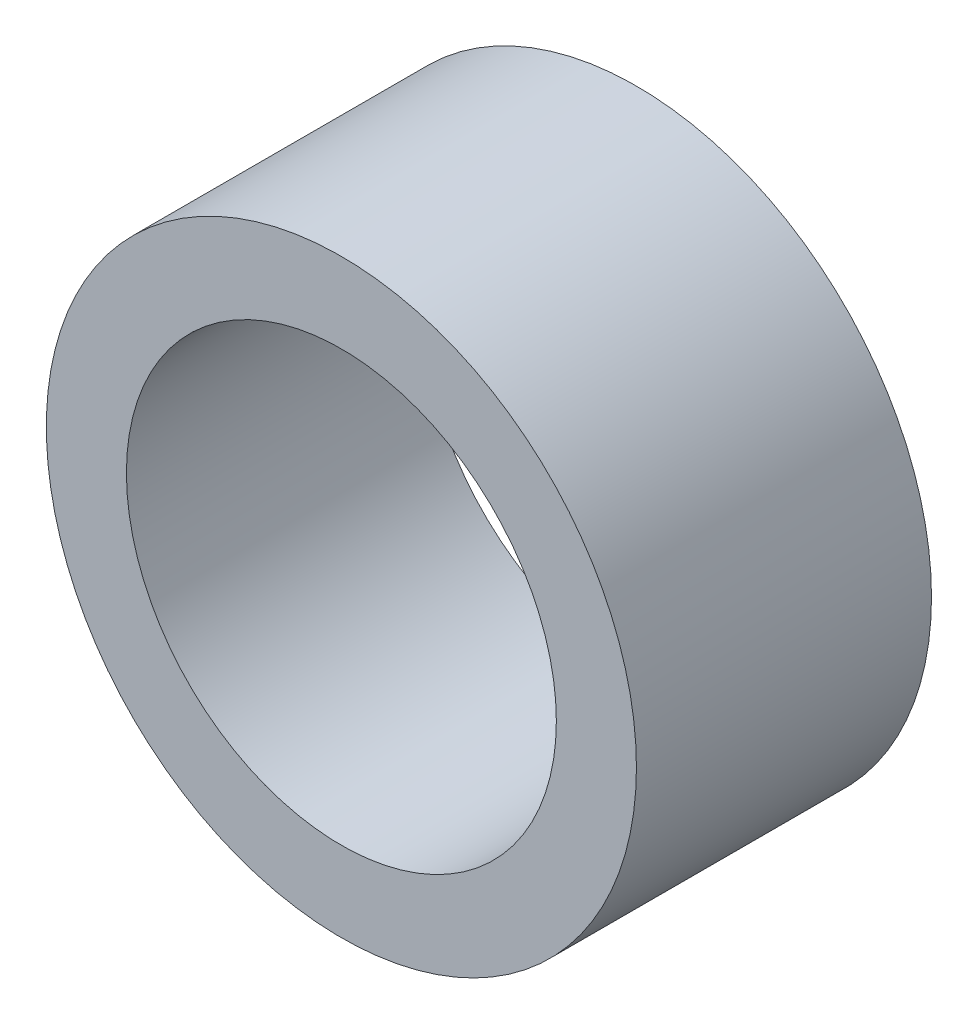
SolidWorks part; units mm, degrees
ref_plane "Front Plane" through (0, 0, 0) normal (0, 0, 1) x (1, 0, 0)
ref_plane "Top Plane" through (0, 0, 0) normal (0, 1, 0) x (1, 0, 0)
ref_plane "Right Plane" through (0, 0, 0) normal (1, 0, 0) x (0, 0, -1)
sketch "Sketch1" plane through (0, 0, 0) normal (0, 0, 1) x (1, 0, 0)
  circle A0 centre (0, 0) radius 3.2385
  circle A1 centre (0, 0) radius 4.445
  dimension "D1" = 6.477
  dimension "D2" = 8.89
extrude "Boss-Extrude1" add sketch "Sketch1" against normal blind 4.445 contours A1
